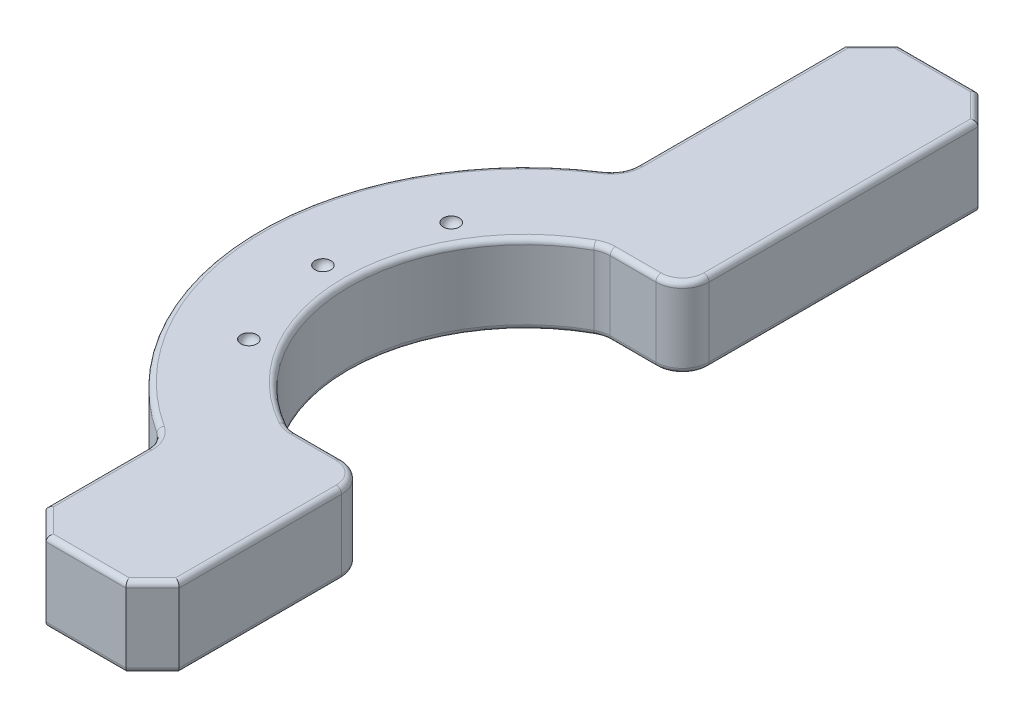
SolidWorks part; units mm, degrees
material "PLA"
ref_plane "Front Plane" through (0, 0, 0) normal (0, 0, 1) x (1, 0, 0)
ref_plane "Top Plane" through (0, 0, 0) normal (0, 1, 0) x (1, 0, 0)
ref_plane "Right Plane" through (0, 0, 0) normal (1, 0, 0) x (0, 0, -1)
sketch "Sketch1" plane through (0, 0, 0) normal (0, 1, 0) x (1, 0, 0)
  line L0 (0, 80) -> (50, 80) construction
  line L1 (0, 0) -> (12.5, 0)
  line L5 (50, 130) -> (50, 113)
  line L6 (50, 47) -> (50, 30)
  arc A0 (50, 113) -> (50, 47) centre (50, 80) ccw
  arc A1 (50, 130) -> (50, 30) centre (50, 80) ccw
  dimension "D2" = 66
  dimension "D3" = 50
extrude "Boss-Extrude2" add sketch "Sketch1" along normal mid plane 15 contours A0 L6 A1 L5
sketch "Sketch2" plane through (50, 0, 0) normal (1, 0, 0) x (0, 0, -1)
  line L0 (47, -7.5) -> (30, -7.5) construction
  line L1 (50.5, 7.5) -> (10, 7.5)
  line L2 (50.5, 7.5) -> (50.5, -7.5)
  line L3 (50.5, -7.5) -> (10, -7.5)
  line L4 (10, 7.5) -> (10, -7.5)
  line L5 (109.5, 7.5) -> (170, 7.5)
  line L6 (109.5, 7.5) -> (109.5, -7.5)
  line L7 (109.5, -7.5) -> (170, -7.5)
  line L8 (170, 7.5) -> (170, -7.5)
  line L9 (130, -7.5) -> (113, -7.5) construction
  line L10 (47, 7.5) -> (47, -7.5) construction
  line L11 (113, 7.5) -> (113, -7.5) construction
  point P14 (0, 0)
  point P15 (0, 0)
  dimension "D1" = 3.5
  dimension "D2" = 3.5
  dimension "D3" = 40.5
  dimension "D4" = 60.5
extrude "Boss-Extrude3" add sketch "Sketch2" against normal blind 25
sketch "Sketch3" plane through (0, 7.5, 0) normal (0, 1, 0) x (1, 0, 0)
  line L0 (12, 81.5) -> (12, 78.5) construction
  line L1 (12, 81.5) -> (12, 78.5)
  arc A1 (12, 81.5) -> (12, 78.5) centre (12, 80) ccw
  dimension "D2" = 3
revolve "Cut-Revolve3" cut sketch "Sketch3" angle 360 about L0
pattern_circular "CirPattern1" count 2 over 30 of "Cut-Revolve3"
pattern_circular "CirPattern2" count 2 over 30 of "Cut-Revolve3"
mirror "Mirror1" about plane through (0, 0, 0) normal (0, 1, 0) of "CirPattern2", "CirPattern1", "Cut-Revolve3"
fillet "Fillet1" radius 5 6 edges at (25, 0, -36.6987) (25, 0, -123.3013) (50, 0, -109.5) (35.2098, 0, -109.5) (35.2098, 0, -50.5) (50, 0, -50.5)
chamfer "Chamfer1" distance 5 angle 45 4 edges at (25, 0, -170) (50, 0, -170) (25, 0, -10) (50, 0, -10)
fillet "Fillet2" radius 1 43 edges at (47.5, -7.5, -167.5) (47.5, 7.5, -167.5) (50, -7.5, -139.75) (50, 7.5, -139.75) (17, -7.5, -80) (17, 7.5, -80) (50, 7.5, -30.25) (50, -7.5, -30.25) (47.5, 7.5, -12.5) (47.5, -7.5, -12.5) (37.5, 7.5, -10) (27.5, 7.5, -12.5) (27.5, -7.5, -12.5) (25, 7.5, -24.4511) (24.3952, -7.5, -36.2859) (24.3952, 7.5, -36.2859) (0, -7.5, -80) (0, 7.5, -80) (24.3952, -7.5, -123.7141) (24.3952, 7.5, -123.7141) (25, 7.5, -145.5489) (27.5, -7.5, -167.5) (27.5, 7.5, -167.5) (37.5, 7.5, -170) (25, -7.5, -24.4511) (37.5, -7.5, -10) (37.5, -7.5, -170) (25, -7.5, -145.5489) (12, -7.5, -78.5) (17.091, -7.5, -59.5) (17.091, -7.5, -97.5) (40.7223, 7.5, -109.5) (40.7223, 7.5, -50.5) (40.7223, -7.5, -50.5) (40.7223, -7.5, -109.5) (48.5355, 7.5, -110.9645) (48.5355, -7.5, -110.9645) (35.1946, 7.5, -109.3412) (35.1946, -7.5, -109.3412) (35.1946, -7.5, -50.6588) (35.1946, 7.5, -50.6588) (48.5355, -7.5, -49.0355) (48.5355, 7.5, -49.0355)
